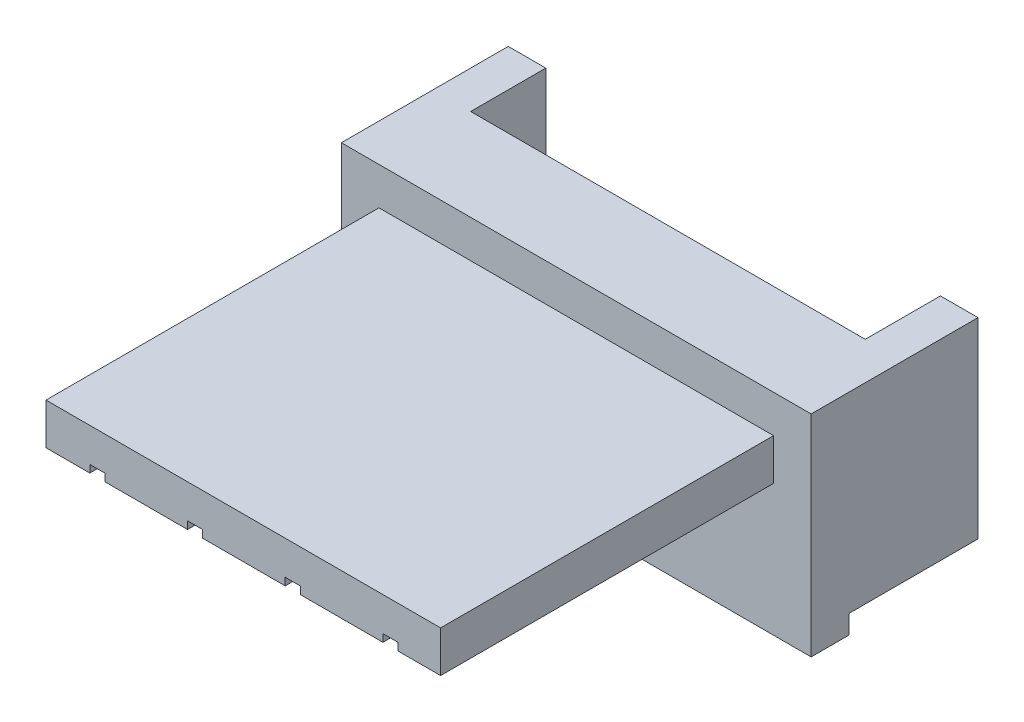
SolidWorks part; units mm, degrees
material "ABS"
ref_plane "Front" through (0, 0, 0) normal (0, 0, 1) x (1, 0, 0)
ref_plane "Top" through (0, 0, 0) normal (0, 1, 0) x (1, 0, 0)
ref_plane "Right" through (0, 0, 0) normal (1, 0, 0) x (0, 0, -1)
sketch "Эскиз1" plane through (0, 0, 0) normal (0, 0, 1) x (1, 0, 0)
  line L0 (-6.25, 5.1) -> (-6.25, 0)
  line L1 (-6.25, 0) -> (0, 0)
  line L2 (-6.25, 5.1) -> (0, 5.1)
  line L3 (0, 5.1) -> (0, 0)
extrude "Бобышка-Вытянуть1" add sketch "Эскиз1" against normal blind 13.3
sketch "Эскиз2" plane through (0, 0, 0) normal (0, -1, 0) x (1, 0, 0)
  line L0 (0, 0) -> (0, -8.86)
  line L1 (0, -13.3) -> (0, 0) construction
  line L2 (0, -8.86) -> (-6.25, -8.86)
  line L3 (-6.25, -13.3) -> (-6.25, 0) construction
  line L4 (-6.25, -8.86) -> (-6.25, 0)
  line L5 (-6.25, 0) -> (0, 0)
extrude "Вырез-Вытянуть1" cut sketch "Эскиз2" against normal blind 3
mirror "Зеркальное отражение1" about plane through (0, 5.1, -13.3) normal (1, 0, 0) of bodies 102
sketch3d "Трехмерный эскиз4"
  line L1 (6.25, 3, 0) -> (-6.25, 3, 0) construction
  line L2 (-3.8844, 3, 0) -> (-3.8844, 3, -13.1)
  line L3 (-3.8844, 3, -13.1) -> (-3.8844, -0.4398, -13.1)
  dimension "D1" = 0.2
sketch "Эскиз6" plane through (0, 0, 0) normal (0, 0, 1) x (1, 0, 0)
  line L1 (-4.0844, 3.2) -> (-3.6844, 3.2)
  line L2 (-4.0844, 3.2) -> (-4.0844, 2.8)
  line L3 (-4.0844, 2.8) -> (-3.6844, 2.8)
  line L4 (-3.6844, 3.2) -> (-3.6844, 2.8)
sketch "Эскиз7" plane through (0, 5.1, 0) normal (0, 1, 0) x (1, 0, 0)
  line L0 (-6.25, 0) -> (-6.25, 8.86)
  line L1 (-6.25, 13.3) -> (-6.25, 0) construction
  line L2 (-6.25, 8.86) -> (6.25, 8.86)
  line L3 (6.25, 13.3) -> (6.25, 0) construction
  line L4 (6.25, 8.86) -> (6.25, 0)
  line L5 (6.25, 0) -> (-6.25, 0)
extrude "Вырез-Вытянуть2" cut sketch "Эскиз7" against normal blind 1
sketch "Эскиз8" plane through (0, 0, 0) normal (0, -1, 0) x (-1, 0, 0)
  line L0 (6.25, 8.86) -> (6.25, 9.8656)
  line L1 (6.25, 13.3) -> (6.25, 8.86) construction
  line L2 (6.25, 9.8656) -> (-6.25, 9.8656)
  line L3 (-6.25, 13.3) -> (-6.25, 8.86) construction
  line L4 (-6.25, 9.8656) -> (-6.25, 8.86)
  line L5 (-6.25, 8.86) -> (6.25, 8.86)
extrude "Бобышка-Вытянуть2" add sketch "Эскиз8" along normal blind 0.5
sketch "Эскиз9" plane through (0, 0, 0) normal (0, 0, 1) x (1, 0, 0)
  line L0 (6.25, 3) -> (5.25, 3)
  line L1 (6.25, 3) -> (-6.25, 3) construction
  line L2 (5.25, 3) -> (5.25, 4.1)
  line L3 (-6.25, 4.1) -> (6.25, 4.1) construction
  line L4 (5.25, 4.1) -> (6.25, 4.1)
  line L5 (6.25, 4.1) -> (6.25, 3)
  line L6 (-6.25, 3) -> (-5.25, 3)
  line L7 (6.25, 3) -> (-6.25, 3) construction
  line L8 (-5.25, 3) -> (-5.25, 4.1)
  line L9 (-5.25, 4.1) -> (-6.25, 4.1)
  line L10 (-6.25, 4.1) -> (-6.25, 3)
extrude "Вырез-Вытянуть3" cut sketch "Эскиз9" against normal blind 8.86
sweep "Вырез-По траектории1" cut profiles "Эскиз6" path "Трехмерный эскиз4"
pattern_linear "Линейный массив1" count 4 spacing 2.6 along (1, 0, 0) of "Вырез-По траектории1"
sketch "Эскиз10" plane through (0, 0, -13.3) normal (0, 0, -1) x (-1, 0, 0)
  line L0 (-6.25, 5.1) -> (6.25, 5.1) construction
  line L1 (-5.25, 5.1) -> (5.25, 5.1)
  line L2 (-5.25, 5.1) -> (-5.25, 2.1)
  line L3 (-5.25, 2.1) -> (5.25, 2.1)
  line L4 (5.25, 5.1) -> (5.25, 2.1)
  line L6 (-6.25, 5.1) -> (-6.25, 0) construction
  line L7 (6.25, 5.1) -> (6.25, 0) construction
  dimension "D1" = 1
  dimension "D2" = 1
  dimension "D3" = 3
extrude "Вырез-Вытянуть4" cut sketch "Эскиз10" against normal blind 2
